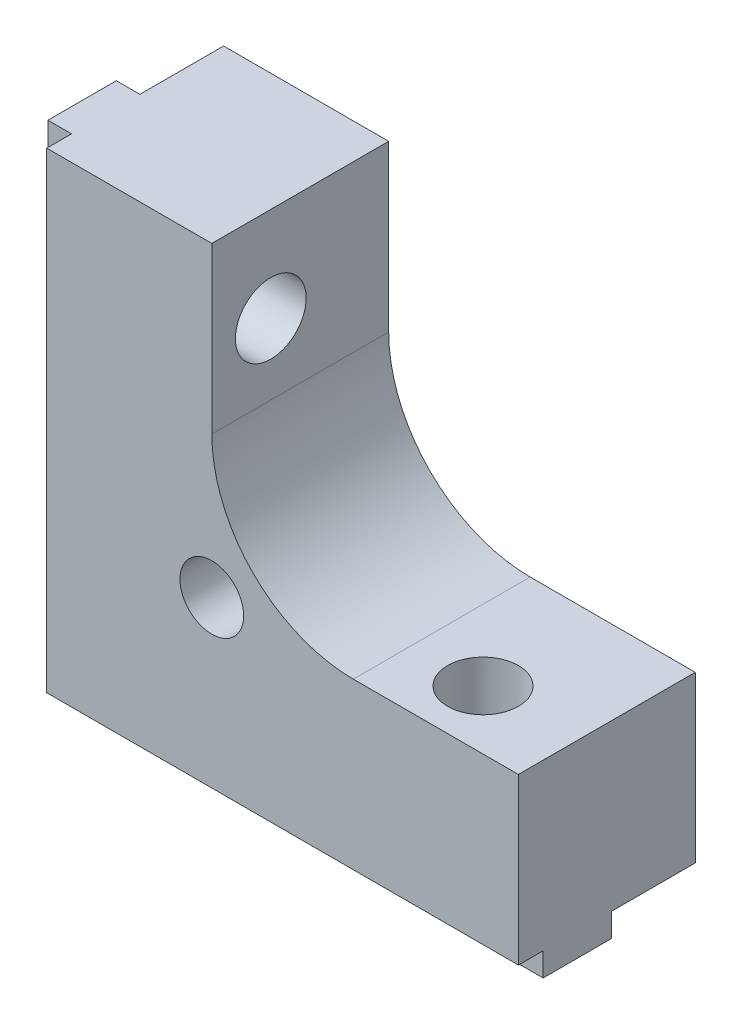
SolidWorks part; units mm, degrees
ref_plane "Front Plane" through (0, 0, 0) normal (0, 0, 1) x (1, 0, 0)
ref_plane "Top Plane" through (0, 0, 0) normal (0, 1, 0) x (1, 0, 0)
ref_plane "Right Plane" through (0, 0, 0) normal (1, 0, 0) x (0, 0, -1)
sketch "Esquisse1" plane through (0, 0, 0) normal (0, 0, 1) x (1, 0, 0)
  line L0 (0, 0) -> (20, 0)
  line L1 (20, 0) -> (20, 7)
  line L2 (20, 7) -> (13, 7)
  line L4 (7, 13) -> (7, 20)
  line L5 (7, 20) -> (0, 20)
  line L6 (0, 20) -> (0, 0)
  arc A0 (13, 7) -> (7, 13) centre (13, 13) cw
  dimension "D1" = 6
  dimension "D2" = 20
  dimension "D3" = 7
  dimension "D4" = 7
  dimension "D5" = 7
extrude "Main" add sketch "Esquisse1" along normal blind 10
sketch "Esquisse4" plane through (0, 0, 0) normal (-1, 0, 0) x (0, 0, 1)
  line L0 (10, 20) -> (0, 20) construction
  line L1 (3.55, 20) -> (6.45, 20)
  line L2 (3.55, 20) -> (3.55, 0)
  line L3 (3.55, 0) -> (6.45, 0)
  line L4 (6.45, 20) -> (6.45, 0)
  line L5 (10, 0) -> (0, 0) construction
  point P8 (5, 20)
  point P9 (5, 20)
  dimension "D1" = 2.9
extrude "MakerBeamFixVertical" add sketch "Esquisse4" along normal blind 1
sketch "Esquisse2" plane through (0, 0, 0) normal (-1, 0, 0) x (0, 0, 1)
  line L0 (10, 20) -> (6.45, 20) construction
  line L1 (10, 20) -> (0, 20) construction
  circle A0 centre (5, 16) radius 1.5
  point P9 (5, 20)
  dimension "D1" = 3
  dimension "D2" = 4
extrude "MakerBeamVerticalHole" cut sketch "Esquisse2" against normal through all both and the other way through all
sketch "Esquisse5" plane through (0, 0, 0) normal (0, -1, 0) x (-1, 0, 0)
  line L0 (-20, -10) -> (-20, 0) construction
  line L1 (0, -3.55) -> (-20, -3.55)
  line L2 (0, -3.55) -> (0, -6.45)
  line L3 (0, -6.45) -> (-20, -6.45)
  line L4 (-20, -3.55) -> (-20, -6.45)
  line L5 (1, -6.45) -> (0, -6.45) construction
extrude "MakerBeamFixHorizontal" add sketch "Esquisse5" along normal blind 1
sketch "Esquisse3" plane through (0, 0, 0) normal (0, -1, 0) x (1, 0, 0)
  line L0 (20, 10) -> (20, 6.45) construction
  line L1 (20, 10) -> (20, 0) construction
  circle A0 centre (16, 5) radius 1.5
  point P2 (20, 5)
  dimension "D1" = 3
  dimension "D2" = 4
extrude "MakerBeamHorizontalHole" cut sketch "Esquisse3" against normal through all both and the other way through all
sketch "Sketch1" plane through (0, 0, 10) normal (0, 0, 1) x (1, 0, 0)
  line L0 (0, 0) -> (20, 0) construction
  line L3 (0, 20) -> (0, 0) construction
  circle A0 centre (7, 7) radius 1.35
  dimension "D1" = 2.7
  dimension "D2" = 7
  dimension "D3" = 7
extrude "WindowFixHole" cut sketch "Sketch1" against normal through all
sketch "Sketch2" plane through (0, 0, 0) normal (-1, 0, 0) x (0, 0, 1)
  line L0 (10, 20) -> (6.45, 20) construction
  line L1 (7.5, 20) -> (10, 20)
  line L2 (7.5, 20) -> (7.5, 0)
  line L3 (7.5, 0) -> (10, 0)
  line L4 (10, 20) -> (10, 0)
  dimension "D1" = 2.5
extrude "Window" cut sketch "Sketch2" against normal through all
